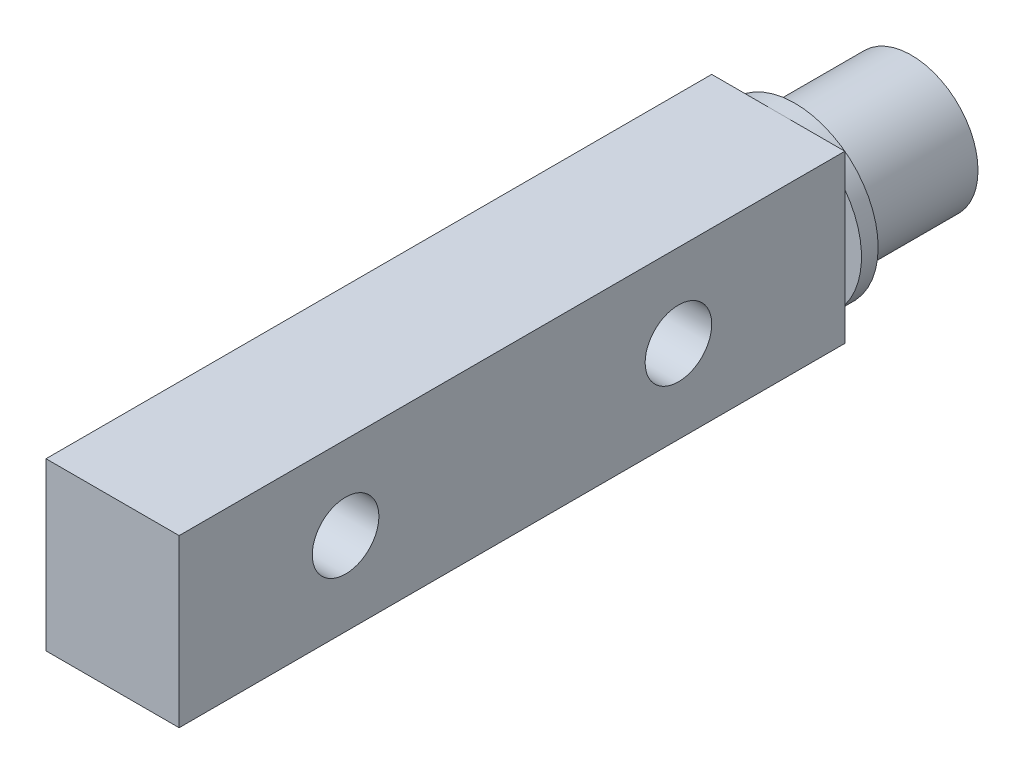
SolidWorks part; units mm, degrees
ref_plane "Спереди" through (0, 0, 0) normal (0, 0, 1) x (1, 0, 0)
ref_plane "Сверху" through (0, 0, 0) normal (0, 1, 0) x (1, 0, 0)
ref_plane "Справа" through (0, 0, 0) normal (1, 0, 0) x (0, 0, -1)
sketch "Эскиз1" plane through (0, 0, 0) normal (0, 0, 1) x (1, 0, 0)
  circle A0 centre (0, 0) radius 4
  dimension "D1" = 8
extrude "Бобышка-Вытянуть1" add sketch "Эскиз1" along normal blind 7
sketch "Эскиз2" plane through (0, 0, 7) normal (0, 0, 1) x (1, 0, 0)
  circle A0 centre (0, 0) radius 5
  dimension "D1" = 10
extrude "Бобышка-Вытянуть2" add sketch "Эскиз2" along normal blind 1
sketch "Эскиз3" plane through (0, 0, 8) normal (0, 0, 1) x (1, 0, 0)
  line L0 (0, 5) -> (0, 0) construction
  line L1 (-4, 5) -> (4, 5)
  line L2 (-4, 5) -> (-4, -5)
  line L3 (-4, -5) -> (4, -5)
  line L4 (4, 5) -> (4, -5)
  line L5 (0, 0) -> (0, -5) construction
  dimension "D1" = 8
  dimension "D2" = 10
extrude "Бобышка-Вытянуть3" add sketch "Эскиз3" along normal blind 40
sketch "Эскиз4" plane through (-4, 0, 0) normal (-1, 0, 0) x (0, 0, 1)
  line L0 (8, 0) -> (48, 0) construction
  line L1 (8, 3) -> (8, -3) construction
  line L2 (48, 5) -> (48, -5) construction
  circle A0 centre (18, 0) radius 2
  circle A1 centre (38, 0) radius 2
  dimension "D1" = 10
  dimension "D2" = 10
  dimension "D3" = 4
extrude "Вырез-Вытянуть1" cut sketch "Эскиз4" against normal up to next
